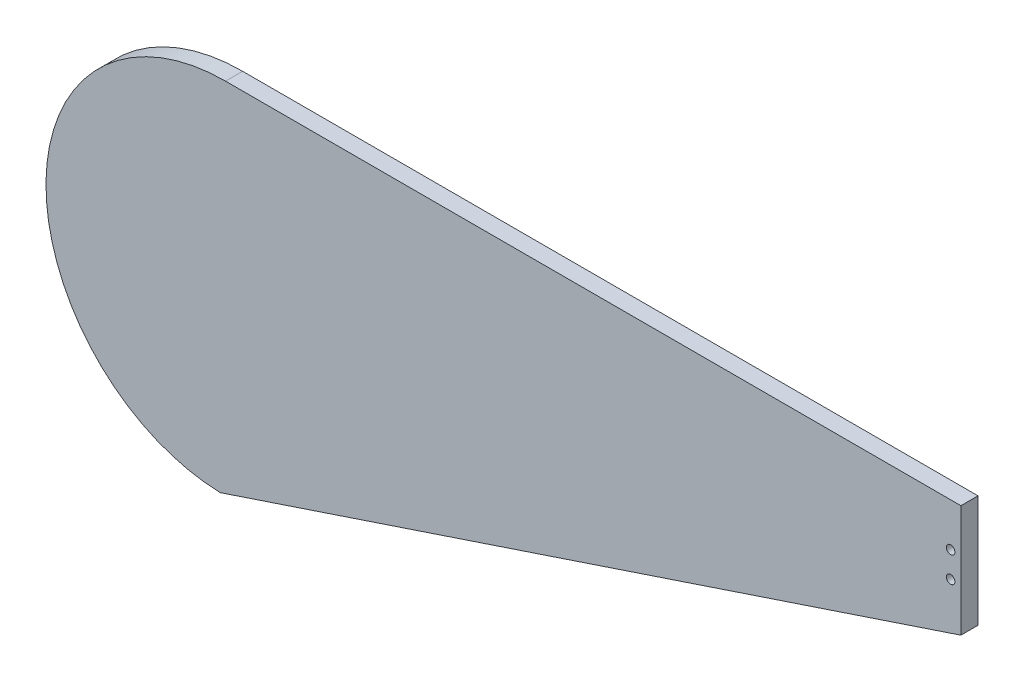
SolidWorks part; units mm, degrees
material "Acrylic (Medium-high impact)"
ref_plane "Front Plane" through (0, 0, 0) normal (0, 0, 1) x (1, 0, 0)
ref_plane "Top Plane" through (0, 0, 0) normal (0, 1, 0) x (1, 0, 0)
ref_plane "Right Plane" through (0, 0, 0) normal (1, 0, 0) x (0, 0, -1)
sketch "Sketch1" plane through (0, 0, 0) normal (0, 0, 1) x (1, 0, 0)
  line L0 (0, -125) -> (450, 25) construction
  line L3 (0, 125) -> (450, 125) construction
  line L4 (450, 25) -> (450, 125) construction
  line L5 (0, 105) -> (430, 105)
  line L6 (430, 39.4152) -> (430, 105)
  line L7 (-3.1076, -104.954) -> (430, 39.4152)
  arc A0 (0, 125) -> (0, -125) centre (0, 0) ccw construction
  arc A1 (0, 105) -> (-3.1076, -104.954) centre (0, 0) ccw
  dimension "D3" = 250
  dimension "D1" = 450
  dimension "D2" = 100
  dimension "D4" = 20
extrude "Boss-Extrude1" add sketch "Sketch1" along normal blind 10
sketch "Sketch2" plane through (0, 0, 10) normal (0, 0, 1) x (1, 0, 0)
  line L0 (430, 39.4152) -> (430, 105) construction
  circle A0 centre (424, 79.7076) radius 2.5
  circle A1 centre (424, 64.7076) radius 2.5
  point P8 (430, 72.2076)
  dimension "D2" = 5
  dimension "D1" = 15
  dimension "D3" = 6
  dimension "D4" = 7.5
extrude "Cut-Extrude1" cut sketch "Sketch2" against normal through all
